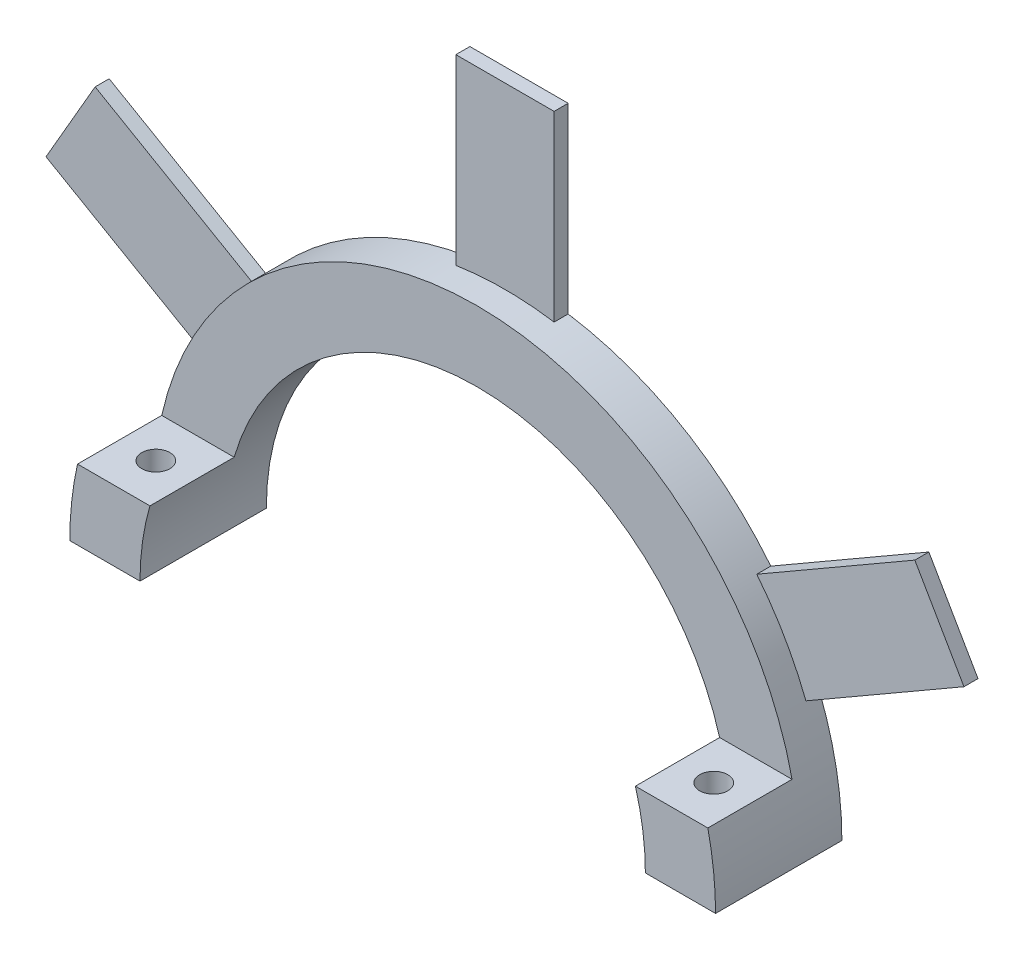
SolidWorks part; units mm, degrees
ref_plane "Front" through (0, 0, 0) normal (0, 0, 1) x (1, 0, 0)
ref_plane "Top" through (0, 0, 0) normal (0, 1, 0) x (1, 0, 0)
ref_plane "Right" through (0, 0, 0) normal (1, 0, 0) x (0, 0, -1)
sketch "Sketch1" plane through (0, 0, 0) normal (0, 0, 1) x (1, 0, 0)
  line L0 (0, 0) -> (0, 35.7321) construction
  line L5 (29.1949, 20.8972) -> (32.6949, 14.835)
  line L6 (-3.5, 35.7321) -> (3.5, 35.7321)
  line L7 (-3.5, 35.7321) -> (-3.5, 22.7321)
  line L9 (3.5, 35.7321) -> (3.5, 22.7321)
  line L10 (-3.5, 35.7321) -> (3.5, 22.7321) construction
  line L11 (-3.5, 22.7321) -> (3.5, 35.7321) construction
  line L12 (29.1949, 20.8972) -> (17.9366, 14.3972)
  line L13 (32.6949, 14.835) -> (21.4366, 8.335)
  line L14 (29.1949, 20.8972) -> (21.4366, 8.335) construction
  line L15 (17.9366, 14.3972) -> (32.6949, 14.835) construction
  line L16 (32.6949, -14.835) -> (29.1949, -20.8972)
  line L17 (32.6949, -14.835) -> (21.4366, -8.335)
  line L18 (29.1949, -20.8972) -> (17.9366, -14.3972)
  line L19 (32.6949, -14.835) -> (17.9366, -14.3972) construction
  line L20 (21.4366, -8.335) -> (29.1949, -20.8972) construction
  line L21 (3.5, -35.7321) -> (-3.5, -35.7321)
  line L22 (3.5, -35.7321) -> (3.5, -22.7321)
  line L23 (-3.5, -35.7321) -> (-3.5, -22.7321)
  line L24 (3.5, -35.7321) -> (-3.5, -22.7321) construction
  line L25 (3.5, -22.7321) -> (-3.5, -35.7321) construction
  line L26 (-29.1949, -20.8972) -> (-32.6949, -14.835)
  line L27 (-29.1949, -20.8972) -> (-17.9366, -14.3972)
  line L28 (-32.6949, -14.835) -> (-21.4366, -8.335)
  line L29 (-29.1949, -20.8972) -> (-21.4366, -8.335) construction
  line L30 (-17.9366, -14.3972) -> (-32.6949, -14.835) construction
  line L31 (-32.6949, 14.835) -> (-29.1949, 20.8972)
  line L32 (-32.6949, 14.835) -> (-21.4366, 8.335)
  line L33 (-29.1949, 20.8972) -> (-17.9366, 14.3972)
  line L34 (-32.6949, 14.835) -> (-17.9366, 14.3972) construction
  line L35 (-21.4366, 8.335) -> (-29.1949, 20.8972) construction
  line L36 (23, 0) -> (-23, 0)
  circle A0 centre (0, 0) radius 23
  circle A1 centre (0, 0) radius 18
  point P4 (0, 29.2321)
  point P10 (25.3158, 14.6161)
  point P17 (25.3158, -14.6161)
  point P22 (0, -29.2321)
  point P27 (-25.3158, -14.6161)
  point P32 (-25.3158, 14.6161)
  dimension "D1" = 46
  dimension "D2" = 36
  dimension "D3" = 13
  dimension "D4" = 7
  dimension "D5" = 6
extrude "Boss-Extrude1" add sketch "Sketch1" along normal blind 3 contours A0 L33 L31 L32 | A1 L36 A0 | A0 L9 L6 L7 | A0 L13 L5 L12
sketch "Sketch2" plane through (0, 0, 3) normal (0, 0, 1) x (1, 0, 0)
  line L0 (-22.4499, 5) -> (-17.2916, 5)
  line L1 (0, 0) -> (0, 18) construction
  line L2 (23, 0) -> (18, 0)
  line L3 (22.4499, 5) -> (17.2916, 5)
  line L11 (-32.6949, 14.835) -> (-21.4366, 8.335)
  line L12 (-23, 0) -> (-18, 0)
  line L13 (18, 0) -> (23, 0)
  line L14 (21.4366, 8.335) -> (32.6949, 14.835)
  line L15 (32.6949, 14.835) -> (29.1949, 20.8972)
  line L16 (29.1949, 20.8972) -> (17.9366, 14.3972)
  line L17 (3.5, 22.7321) -> (3.5, 35.7321)
  line L18 (3.5, 35.7321) -> (-3.5, 35.7321)
  line L19 (-3.5, 35.7321) -> (-3.5, 22.7321)
  line L20 (-17.9366, 14.3972) -> (-29.1949, 20.8972)
  line L21 (-29.1949, 20.8972) -> (-32.6949, 14.835)
  line L22 (-32.6949, 14.835) -> (-21.4366, 8.335)
  line L23 (-23, 0) -> (-18, 0)
  line L24 (18, 0) -> (23, 0)
  line L25 (21.4366, 8.335) -> (32.6949, 14.835)
  line L26 (32.6949, 14.835) -> (29.1949, 20.8972)
  line L27 (29.1949, 20.8972) -> (17.9366, 14.3972)
  line L28 (3.5, 22.7321) -> (3.5, 35.7321)
  line L29 (3.5, 35.7321) -> (-3.5, 35.7321)
  line L30 (-3.5, 35.7321) -> (-3.5, 22.7321)
  line L31 (-17.9366, 14.3972) -> (-29.1949, 20.8972)
  line L32 (-29.1949, 20.8972) -> (-32.6949, 14.835)
  arc A5 (-21.4366, 8.335) -> (-23, 0) centre (0, 0) ccw
  arc A6 (18, 0) -> (-18, 0) centre (0, 0) ccw
  arc A7 (23, 0) -> (21.4366, 8.335) centre (0, 0) ccw
  arc A8 (17.9366, 14.3972) -> (3.5, 22.7321) centre (0, 0) ccw
  arc A9 (-3.5, 22.7321) -> (-17.9366, 14.3972) centre (0, 0) ccw
  arc A10 (-21.4366, 8.335) -> (-23, 0) centre (0, 0) ccw
  arc A11 (18, 0) -> (-18, 0) centre (0, 0) ccw
  arc A12 (23, 0) -> (21.4366, 8.335) centre (0, 0) ccw
  arc A13 (17.9366, 14.3972) -> (3.5, 22.7321) centre (0, 0) ccw
  arc A14 (-3.5, 22.7321) -> (-17.9366, 14.3972) centre (0, 0) ccw
  arc M20 (-21.4366, 8.335) -> (-23, 0) centre (0, 0) ccw
  line M21 (-23, 0) -> (-18, 0)
  arc M22 (-18, 0) -> (18, 0) centre (0, 0) cw
  line M23 (18, 0) -> (23, 0)
  arc M24 (23, 0) -> (21.4366, 8.335) centre (0, 0) ccw
  dimension "D2" = 5
  dimension "D1" = 0
extrude "Boss-Extrude2" add sketch "Sketch2" along normal blind 6 contours L0 M20 M21 M22 | L3 M24 M22 M23
sketch "Sketch4" plane through (0, 5, 0) normal (0, 1, 0) x (1, 0, 0)
  line L0 (-19.8708, -9) -> (-19.8708, -3) construction
  line L1 (-22.4499, -9) -> (-17.2916, -9) construction
  line L2 (-22.4499, -3) -> (-17.2916, -3) construction
  line L3 (-22.4499, -6) -> (-17.2916, -6) construction
  line L4 (-22.4499, -9) -> (-22.4499, -3) construction
  line L5 (-17.2916, -9) -> (-17.2916, -3) construction
  line L6 (0, 0) -> (0, -45.9104) construction
  line L7 (22.4499, -6) -> (17.2916, -6) construction
  line L8 (19.8708, -9) -> (19.8708, -3) construction
  circle A0 centre (-19.8708, -6) radius 1
  circle A1 centre (19.8708, -6) radius 1
  dimension "D1" = 2
extrude "Cut-Extrude1" cut sketch "Sketch4" against normal blind 5
sketch "Sketch5" plane through (0, 0, 3) normal (0, 0, 1) x (1, 0, 0)
  line L11 (17.2916, 5) -> (22.4499, 5)
  line L12 (21.4366, 8.335) -> (32.6949, 14.835)
  line L13 (32.6949, 14.835) -> (29.1949, 20.8972)
  line L14 (29.1949, 20.8972) -> (17.9366, 14.3972)
  line L15 (3.5, 22.7321) -> (3.5, 35.7321)
  line L16 (3.5, 35.7321) -> (-3.5, 35.7321)
  line L17 (-3.5, 35.7321) -> (-3.5, 22.7321)
  line L18 (-17.9366, 14.3972) -> (-29.1949, 20.8972)
  line L19 (-29.1949, 20.8972) -> (-32.6949, 14.835)
  line L20 (-32.6949, 14.835) -> (-21.4366, 8.335)
  line L21 (-22.4499, 5) -> (-17.2916, 5)
  line L22 (17.2916, 5) -> (22.4499, 5)
  line L23 (21.4366, 8.335) -> (32.6949, 14.835)
  line L24 (32.6949, 14.835) -> (29.1949, 20.8972)
  line L25 (29.1949, 20.8972) -> (17.9366, 14.3972)
  line L26 (3.5, 22.7321) -> (3.5, 35.7321)
  line L27 (3.5, 35.7321) -> (-3.5, 35.7321)
  line L28 (-3.5, 35.7321) -> (-3.5, 22.7321)
  line L29 (-17.9366, 14.3972) -> (-29.1949, 20.8972)
  line L30 (-29.1949, 20.8972) -> (-32.6949, 14.835)
  line L31 (-32.6949, 14.835) -> (-21.4366, 8.335)
  line L32 (-22.4499, 5) -> (-17.2916, 5)
  circle A0 centre (0, 0) radius 23
  arc A5 (17.2916, 5) -> (-17.2916, 5) centre (0, 0) ccw
  arc A6 (22.4499, 5) -> (21.4366, 8.335) centre (0, 0) ccw
  arc A7 (17.9366, 14.3972) -> (3.5, 22.7321) centre (0, 0) ccw
  arc A8 (-3.5, 22.7321) -> (-17.9366, 14.3972) centre (0, 0) ccw
  arc A9 (-21.4366, 8.335) -> (-22.4499, 5) centre (0, 0) ccw
  arc A10 (17.2916, 5) -> (-17.2916, 5) centre (0, 0) ccw
  arc A11 (22.4499, 5) -> (21.4366, 8.335) centre (0, 0) ccw
  arc A12 (17.9366, 14.3972) -> (3.5, 22.7321) centre (0, 0) ccw
  arc A13 (-3.5, 22.7321) -> (-17.9366, 14.3972) centre (0, 0) ccw
  arc A14 (-21.4366, 8.335) -> (-22.4499, 5) centre (0, 0) ccw
  line M20 (21.4366, 8.335) -> (32.6949, 14.835)
  line M21 (32.6949, 14.835) -> (29.1949, 20.8972)
  line M22 (29.1949, 20.8972) -> (17.9366, 14.3972)
  line M24 (3.5, 22.7321) -> (3.5, 35.7321)
  line M25 (3.5, 35.7321) -> (-3.5, 35.7321)
  line M26 (-3.5, 35.7321) -> (-3.5, 22.7321)
  line M28 (-17.9366, 14.3972) -> (-29.1949, 20.8972)
  line M29 (-29.1949, 20.8972) -> (-32.6949, 14.835)
  line M30 (-32.6949, 14.835) -> (-21.4366, 8.335)
  dimension "D1" = 0
extrude "Cut-Extrude2" cut sketch "Sketch5" against normal blind 2 contours A0 M28 M29 M30 | A0 M24 M25 M26 | A0 M20 M21 M22
equation "\"Buite_DIA\"= \"BInnen_DIA\" + 10"
equation "\"BInnen_DIA\" = 36"
equation "\"Buite_DIa-Uitreksel\" = 13"
equation "\"Breedte_uitreksel\" = 7"
equation "\"Breedte_schroefgat\" = 6"
equation "\"Hoogte_schroefgat\"= 6"
equation "\"Dia_schroefgat\"= 2"
